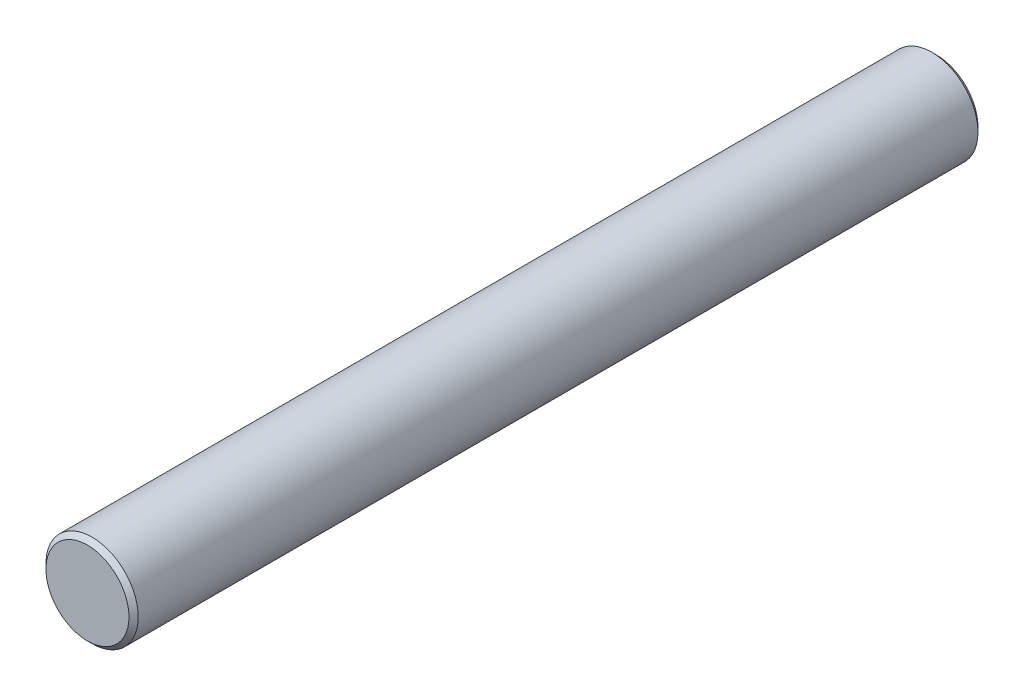
SolidWorks part; units mm, degrees
ref_plane "Piano frontale" through (0, 0, 0) normal (0, 0, 1) x (1, 0, 0)
ref_plane "Piano superiore" through (0, 0, 0) normal (0, 1, 0) x (1, 0, 0)
ref_plane "Piano destro" through (0, 0, 0) normal (1, 0, 0) x (0, 0, -1)
sketch "Schizzo1" plane through (0, 0, 0) normal (0, 0, 1) x (1, 0, 0)
  circle A0 centre (0, 0) radius 2.5
  dimension "D1" = 5
extrude "Estrusione-Estrusione1" add sketch "Schizzo1" along normal blind 46
chamfer "Smusso1" distance 0.25 angle 45 2 edges at (2.5, 0, 46) (2.5, 0, 0)
